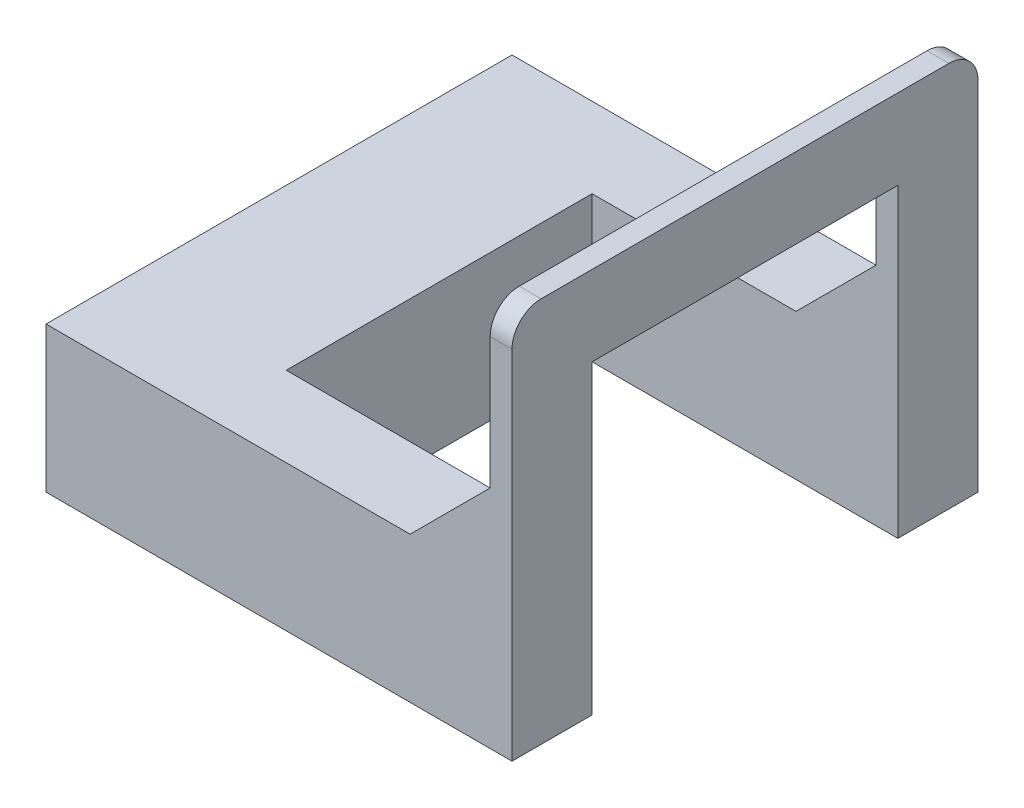
SolidWorks part; units mm, degrees
ref_plane "前视基准面" through (0, 0, 0) normal (0, 0, 1) x (1, 0, 0)
ref_plane "上视基准面" through (0, 0, 0) normal (0, 1, 0) x (1, 0, 0)
ref_plane "右视基准面" through (0, 0, 0) normal (1, 0, 0) x (0, 0, -1)
sketch "草图1" plane through (0, 0, 0) normal (0, 1, 0) x (1, 0, 0)
  line L0 (0, 160) -> (110, 160) construction
  line L1 (0, 0) -> (320, 0)
  line L2 (0, 0) -> (0, 320)
  line L3 (0, 320) -> (320, 320)
  line L4 (320, 0) -> (320, 320) construction
  line L5 (320, 320) -> (320, 265)
  line L6 (320, 265) -> (110, 265)
  line L7 (110, 265) -> (110, 55)
  line L8 (110, 55) -> (320, 55)
  line L9 (320, 55) -> (320, 0)
  dimension "D1" = 320
  dimension "D2" = 210
extrude "凸台-拉伸1" add sketch "草图1" along normal blind 100
sketch "草图2" plane through (320, 0, 0) normal (1, 0, 0) x (0, 0, -1)
  line L0 (0, 0) -> (0, 265)
  line L1 (0, 265) -> (320, 265)
  line L2 (320, 265) -> (320, 0)
  line L3 (0, 0) -> (55, 0)
  line L4 (55, 0) -> (55, 210)
  line L5 (55, 210) -> (265, 210)
  line L6 (265, 210) -> (265, 0)
  line L7 (265, 100) -> (265, 0) construction
  line L8 (265, 0) -> (320, 0)
  line L9 (55, 210) -> (55, 265) construction
  dimension "D1" = 210
  dimension "D2" = 55
extrude "凸台-拉伸2" add sketch "草图2" against normal blind 15
sketch "草图3" plane through (0, 0, 0) normal (0, 0, 1) x (1, 0, 0)
  line L0 (250, 100) -> (305, 100)
  line L1 (0, 100) -> (305, 100) construction
  line L2 (305, 100) -> (305, 155)
  line L3 (305, 265) -> (305, 100) construction
  line L4 (305, 155) -> (250, 100)
  dimension "D1" = 55
extrude "凸台-拉伸3" add sketch "草图3" against normal blind 55
sketch "草图4" plane through (0, 0, -320) normal (0, 0, -1) x (-1, 0, 0)
  line L0 (-305, 155) -> (-305, 100)
  line L1 (-305, 100) -> (-305, 265) construction
  line L2 (-305, 100) -> (-250, 100)
  line L3 (-305, 100) -> (0, 100) construction
  line L4 (-250, 100) -> (-305, 155)
  dimension "D1" = 55
extrude "凸台-拉伸4" add sketch "草图4" against normal blind 55
fillet "圆角1" radius 20 2 edges at (312.5, 265, 0) (312.5, 265, -320)
